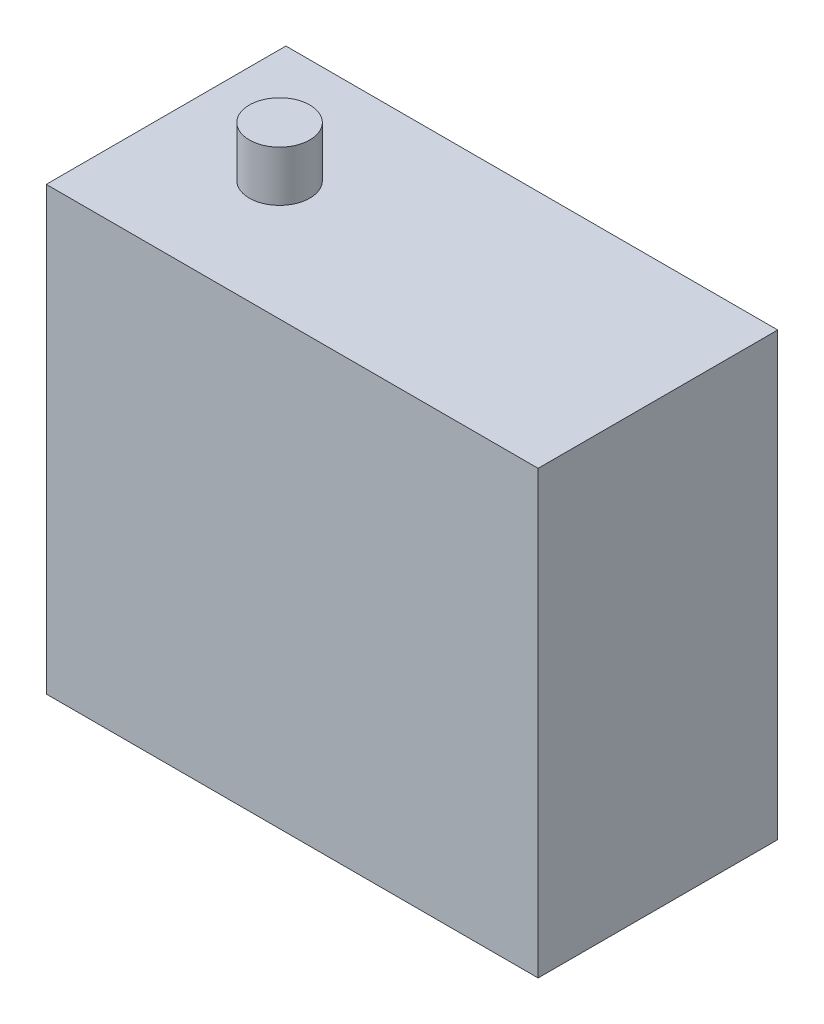
SolidWorks part; units mm, degrees
ref_plane "Front Plane" through (0, 0, 0) normal (0, 0, 1) x (1, 0, 0)
ref_plane "Top Plane" through (0, 0, 0) normal (0, 1, 0) x (1, 0, 0)
ref_plane "Right Plane" through (0, 0, 0) normal (1, 0, 0) x (0, 0, -1)
sketch "Sketch1" plane through (0, 0, 0) normal (0, 1, 0) x (1, 0, 0)
  line L1 (19.5, -9.5) -> (-19.5, -9.5)
  line L2 (19.5, -9.5) -> (19.5, 9.5)
  line L3 (19.5, 9.5) -> (-19.5, 9.5)
  line L4 (-19.5, -9.5) -> (-19.5, 9.5)
  line L5 (19.5, -9.5) -> (-19.5, 9.5) construction
  line L6 (19.5, 9.5) -> (-19.5, -9.5) construction
  point P0 (0, 0)
  dimension "D1" = 19
  dimension "D2" = 39
extrude "Boss-Extrude1" add sketch "Sketch1" along normal blind 35
sketch "Sketch2" plane through (0, 35, 0) normal (0, 1, 0) x (1, 0, 0)
  line L0 (19.5, -9.5) -> (19.5, 9.5) construction
  circle A0 centre (-10.5, 0) radius 2.4
  dimension "D2" = 4.8
  dimension "D1" = 30
extrude "Boss-Extrude2" add sketch "Sketch2" along normal blind 4
